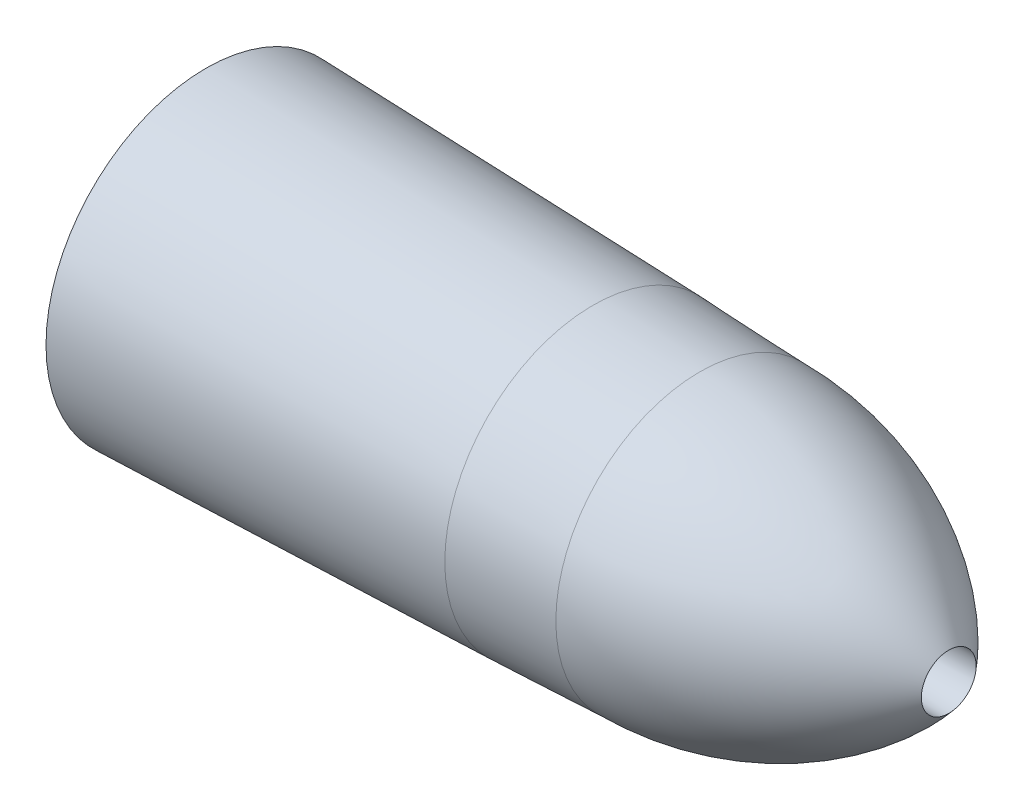
SolidWorks part; units mm, degrees
ref_plane "Front Plane" through (0, 0, 0) normal (0, 0, 1) x (1, 0, 0)
ref_plane "Top Plane" through (0, 0, 0) normal (0, 1, 0) x (1, 0, 0)
ref_plane "Right Plane" through (0, 0, 0) normal (1, 0, 0) x (0, 0, -1)
sketch "Sketch1" plane through (0, 0, 0) normal (0, 1, 0) x (1, 0, 0)
  line L0 (-69.2905, 0) -> (51.3822, 0) construction
  line L1 (-355, -76.3944) -> (-355, 76.3944)
  line L2 (-170, 70.8239) -> (-170, -70.8239)
  line L3 (-119, 68.7549) -> (-119, -68.7549)
  line L4 (-355, 76.3944) -> (-170, 70.8239)
  line L5 (-119, 68.7549) -> (-170, 70.8239)
  line L6 (-355, -76.3944) -> (-170, -70.8239)
  line L7 (-119, -68.7549) -> (-170, -70.8239)
  line L8 (-355, -12.3) -> (-355, 12.3)
  line L9 (0, 13.1) -> (0, -13.1)
  line L10 (-355, 12.3) -> (0, 13.1)
  line L11 (0, -13.1) -> (-355, -12.3)
  arc A0 (-119, 68.7549) -> (0, 13.1) centre (-119, -86.294) cw
  arc A1 (-119, -68.7549) -> (0, -13.1) centre (-125.8876, 101.0209) ccw
  point P6 (-355, 0)
  point P9 (-170, 0)
  point P12 (-119, 0)
  point P15 (-355, 0)
  point P18 (0, 0)
  dimension "D1" = 152.7887
  dimension "D2" = 355
  dimension "D3" = 141.6479
  dimension "D4" = 137.5099
  dimension "D5" = 185
  dimension "D6" = 236
  dimension "D7" = 24.6
  dimension "D8" = 26.2
revolve "Revolve1" add sketch "Sketch1" angle 360 about L0
